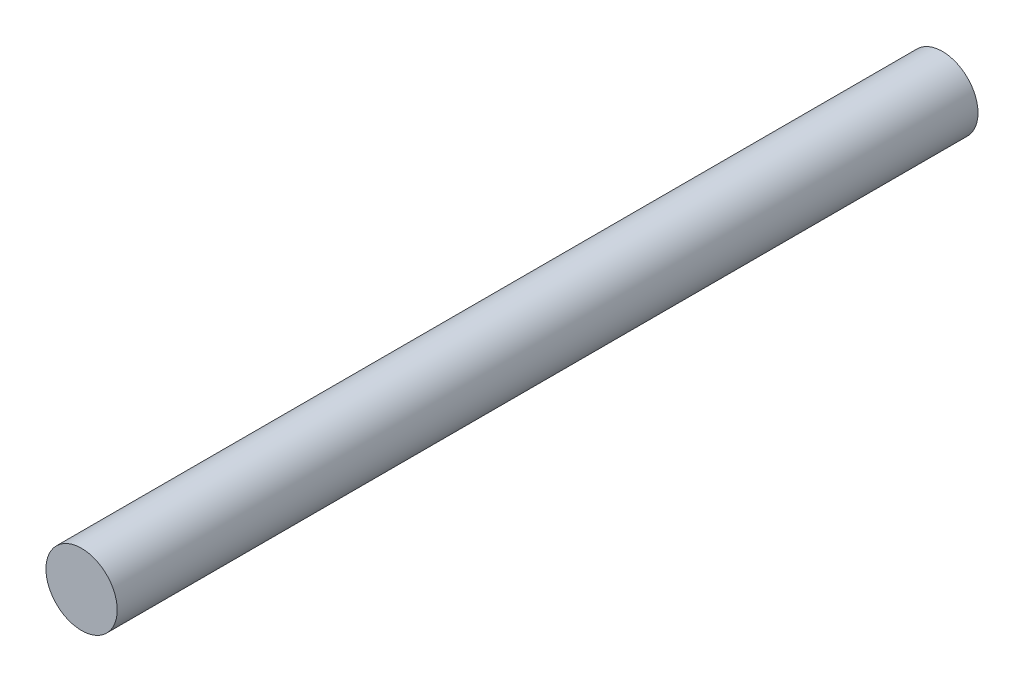
SolidWorks part; units mm, degrees
ref_plane "Front Plane" through (0, 0, 0) normal (0, 0, 1) x (1, 0, 0)
ref_plane "Top Plane" through (0, 0, 0) normal (0, 1, 0) x (1, 0, 0)
ref_plane "Right Plane" through (0, 0, 0) normal (1, 0, 0) x (0, 0, -1)
sketch "Sketch1" plane through (0, 0, 0) normal (0, 0, 1) x (1, 0, 0)
  circle A0 centre (0, 0) radius 2.6289
  dimension "D1" = 5.2578
extrude "Boss-Extrude1" add sketch "Sketch1" along normal blind 63.5
equation "\"D1@Boss-Extrude1\" = 2.5"
